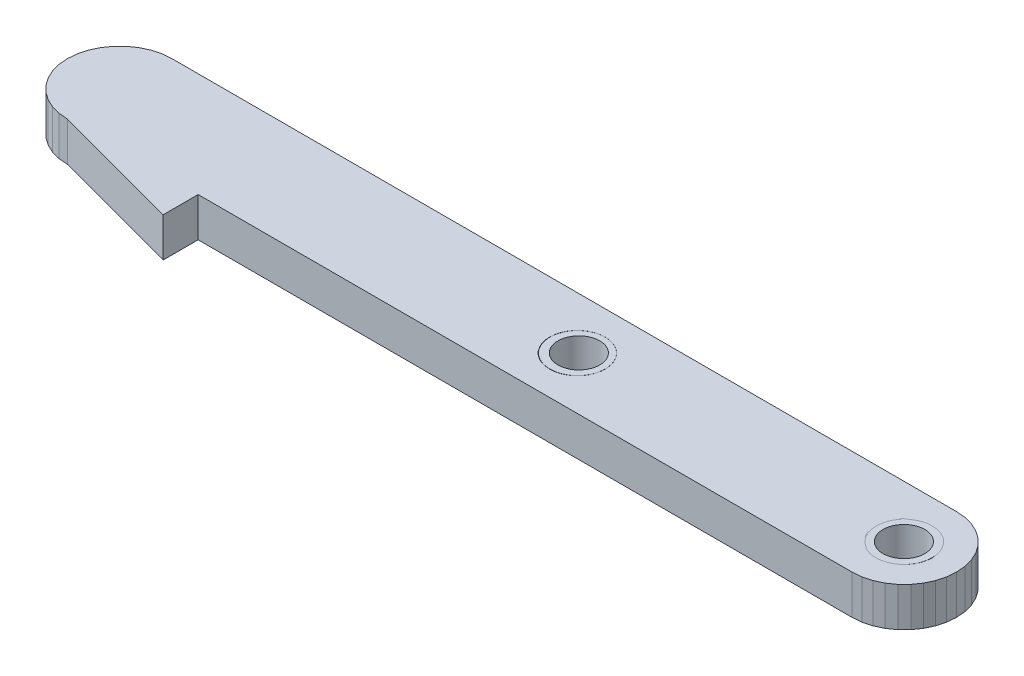
SolidWorks part; units mm, degrees
ref_plane "Front Plane" through (0, 0, 0) normal (0, 0, 1) x (1, 0, 0)
ref_plane "Top Plane" through (0, 0, 0) normal (0, 1, 0) x (1, 0, 0)
ref_plane "Right Plane" through (0, 0, 0) normal (1, 0, 0) x (0, 0, -1)
ref_plane "Plane1" through (0, 0, 0) normal (0, -1, 0) x (1, 0, 0)
sketch "Sketch1" plane through (0, 0, 0) normal (0, -1, 0) x (1, 0, 0)
  line L0 (62.6341, 2.3722) -> (62.3722, 2.6341)
  line L1 (62.3722, 2.6341) -> (62.1597, 2.9375)
  line L2 (62.1597, 2.9375) -> (62.0032, 3.2732)
  line L3 (62.0032, 3.2732) -> (61.9073, 3.631)
  line L4 (61.9073, 3.631) -> (61.875, 4)
  line L5 (61.875, 4) -> (61.9073, 4.369)
  line L6 (61.9073, 4.369) -> (62.0032, 4.7268)
  line L7 (62.0032, 4.7268) -> (62.1597, 5.0625)
  line L8 (62.1597, 5.0625) -> (62.3722, 5.3659)
  line L9 (62.3722, 5.3659) -> (62.6341, 5.6278)
  line L10 (62.6341, 5.6278) -> (62.9375, 5.8403)
  line L11 (62.9375, 5.8403) -> (63.2732, 5.9968)
  line L12 (63.2732, 5.9968) -> (63.631, 6.0927)
  line L13 (63.631, 6.0927) -> (64, 6.125)
  line L14 (64, 6.125) -> (64.369, 6.0927)
  line L15 (64.369, 6.0927) -> (64.7268, 5.9968)
  line L16 (64.7268, 5.9968) -> (65.0625, 5.8403)
  line L17 (65.0625, 5.8403) -> (65.3659, 5.6278)
  line L18 (65.3659, 5.6278) -> (65.6278, 5.3659)
  line L19 (65.6278, 5.3659) -> (65.8403, 5.0625)
  line L20 (65.8403, 5.0625) -> (65.9968, 4.7268)
  line L21 (65.9968, 4.7268) -> (66.0927, 4.369)
  line L22 (66.0927, 4.369) -> (66.125, 4)
  line L23 (66.125, 4) -> (66.0927, 3.631)
  line L24 (66.0927, 3.631) -> (65.9968, 3.2732)
  line L25 (65.9968, 3.2732) -> (65.8403, 2.9375)
  line L26 (65.8403, 2.9375) -> (65.6278, 2.6341)
  line L27 (65.6278, 2.6341) -> (65.3659, 2.3722)
  line L28 (65.3659, 2.3722) -> (65.0625, 2.1597)
  line L29 (65.0625, 2.1597) -> (64.7268, 2.0032)
  line L30 (64.7268, 2.0032) -> (64.369, 1.9073)
  line L31 (64.369, 1.9073) -> (64, 1.875)
  line L32 (64, 1.875) -> (63.631, 1.9073)
  line L33 (63.631, 1.9073) -> (63.2732, 2.0032)
  line L34 (63.2732, 2.0032) -> (62.9375, 2.1597)
  line L35 (62.9375, 2.1597) -> (62.6341, 2.3722)
  line L36 (64, 8) -> (14, 8)
  line L37 (14, 8) -> (14, 10.6795)
  line L38 (14, 10.6795) -> (4, 8)
  line L39 (4, 8) -> (3.3054, 7.9392)
  line L40 (3.3054, 7.9392) -> (2.6319, 7.7588)
  line L41 (2.6319, 7.7588) -> (2, 7.4641)
  line L42 (2, 7.4641) -> (1.4288, 7.0642)
  line L43 (1.4288, 7.0642) -> (0.9358, 6.5712)
  line L44 (0.9358, 6.5712) -> (0.5359, 6)
  line L45 (0.5359, 6) -> (0.2412, 5.3681)
  line L46 (0.2412, 5.3681) -> (0.0608, 4.6946)
  line L47 (0.0608, 4.6946) -> (0, 4)
  line L48 (0, 4) -> (0.0608, 3.3054)
  line L49 (0.0608, 3.3054) -> (0.2412, 2.6319)
  line L50 (0.2412, 2.6319) -> (0.5359, 2)
  line L51 (0.5359, 2) -> (0.9358, 1.4288)
  line L52 (0.9358, 1.4288) -> (1.4288, 0.9358)
  line L53 (1.4288, 0.9358) -> (2, 0.5359)
  line L54 (2, 0.5359) -> (2.6319, 0.2412)
  line L55 (2.6319, 0.2412) -> (3.3054, 0.0608)
  line L56 (3.3054, 0.0608) -> (4, 0)
  line L57 (4, 0) -> (64, 0)
  line L58 (64, 0) -> (64.6946, 0.0608)
  line L59 (64.6946, 0.0608) -> (65.3681, 0.2412)
  line L60 (65.3681, 0.2412) -> (66, 0.5359)
  line L61 (66, 0.5359) -> (66.5712, 0.9358)
  line L62 (66.5712, 0.9358) -> (67.0642, 1.4288)
  line L63 (67.0642, 1.4288) -> (67.4641, 2)
  line L64 (67.4641, 2) -> (67.7588, 2.6319)
  line L65 (67.7588, 2.6319) -> (67.9392, 3.3054)
  line L66 (67.9392, 3.3054) -> (68, 4)
  line L67 (68, 4) -> (67.9392, 4.6946)
  line L68 (67.9392, 4.6946) -> (67.7588, 5.3681)
  line L69 (67.7588, 5.3681) -> (67.4641, 6)
  line L70 (67.4641, 6) -> (67.0642, 6.5712)
  line L71 (67.0642, 6.5712) -> (66.5712, 7.0642)
  line L72 (66.5712, 7.0642) -> (66, 7.4641)
  line L73 (66, 7.4641) -> (65.3681, 7.7588)
  line L74 (65.3681, 7.7588) -> (64.6946, 7.9392)
  line L75 (64.6946, 7.9392) -> (64, 8)
  line L76 (38.2732, 5.9968) -> (38.631, 6.0927)
  line L77 (38.631, 6.0927) -> (39, 6.125)
  line L78 (39, 6.125) -> (39.369, 6.0927)
  line L79 (39.369, 6.0927) -> (39.7268, 5.9968)
  line L80 (39.7268, 5.9968) -> (40.0625, 5.8403)
  line L81 (40.0625, 5.8403) -> (40.3659, 5.6278)
  line L82 (40.3659, 5.6278) -> (40.6278, 5.3659)
  line L83 (40.6278, 5.3659) -> (40.8403, 5.0625)
  line L84 (40.8403, 5.0625) -> (40.9968, 4.7268)
  line L85 (40.9968, 4.7268) -> (41.0927, 4.369)
  line L86 (41.0927, 4.369) -> (41.125, 4)
  line L87 (41.125, 4) -> (41.0927, 3.631)
  line L88 (41.0927, 3.631) -> (40.9968, 3.2732)
  line L89 (40.9968, 3.2732) -> (40.8403, 2.9375)
  line L90 (40.8403, 2.9375) -> (40.6278, 2.6341)
  line L91 (40.6278, 2.6341) -> (40.3659, 2.3722)
  line L92 (40.3659, 2.3722) -> (40.0625, 2.1597)
  line L93 (40.0625, 2.1597) -> (39.7268, 2.0032)
  line L94 (39.7268, 2.0032) -> (39.369, 1.9073)
  line L95 (39.369, 1.9073) -> (39, 1.875)
  line L96 (39, 1.875) -> (38.631, 1.9073)
  line L97 (38.631, 1.9073) -> (38.2732, 2.0032)
  line L98 (38.2732, 2.0032) -> (37.9375, 2.1597)
  line L99 (37.9375, 2.1597) -> (37.6341, 2.3722)
  line L100 (37.6341, 2.3722) -> (37.3722, 2.6341)
  line L101 (37.3722, 2.6341) -> (37.1597, 2.9375)
  line L102 (37.1597, 2.9375) -> (37.0032, 3.2732)
  line L103 (37.0032, 3.2732) -> (36.9073, 3.631)
  line L104 (36.9073, 3.631) -> (36.875, 4)
  line L105 (36.875, 4) -> (36.9073, 4.369)
  line L106 (36.9073, 4.369) -> (37.0032, 4.7268)
  line L107 (37.0032, 4.7268) -> (37.1597, 5.0625)
  line L108 (37.1597, 5.0625) -> (37.3722, 5.3659)
  line L109 (37.3722, 5.3659) -> (37.6341, 5.6278)
  line L110 (37.6341, 5.6278) -> (37.9375, 5.8403)
  line L111 (37.9375, 5.8403) -> (38.2732, 5.9968)
extrude "Boss-Extrude1" add sketch "Sketch1" against normal blind 3
sketch "Sketch2" plane through (0, 3, 0) normal (0, 1, 0) x (1, 0, 0)
  circle A0 centre (39.0037, -3.9946) radius 2.1112
  circle A1 centre (63.9652, -3.9946) radius 2.1492
extrude "Boss-Extrude2" add sketch "Sketch2" against normal blind 3 separate body
hole_wizard "M3 Clearance Hole1" positions "Sketch3" profile "Sketch4" hole size "M3" standard "ANSI Metric" end condition through all
sketch "Sketch3" plane through (0, 3, 0) normal (0, 1, 0) x (1, 0, 0)
  point P0 (39.0426, -3.9315)
  point P2 (63.9652, -3.9946)
sketch "Sketch4" plane through (39.0426, 3, 3.9315) normal (1, 0, 0) x (0, 0, 1)
  line L0 (0, 0) -> (0, 3)
  line L1 (0, 3) -> (1.6, 3)
  line L2 (1.6, 3) -> (1.6, 0)
  line L5 (1.6, 0) -> (0, 0)
  line L11 (0, -6.35) -> (0, 107.95) construction
  dimension "Thru Hole Dia." = 3.2
  dimension "Thru Hole Depth" = 3
